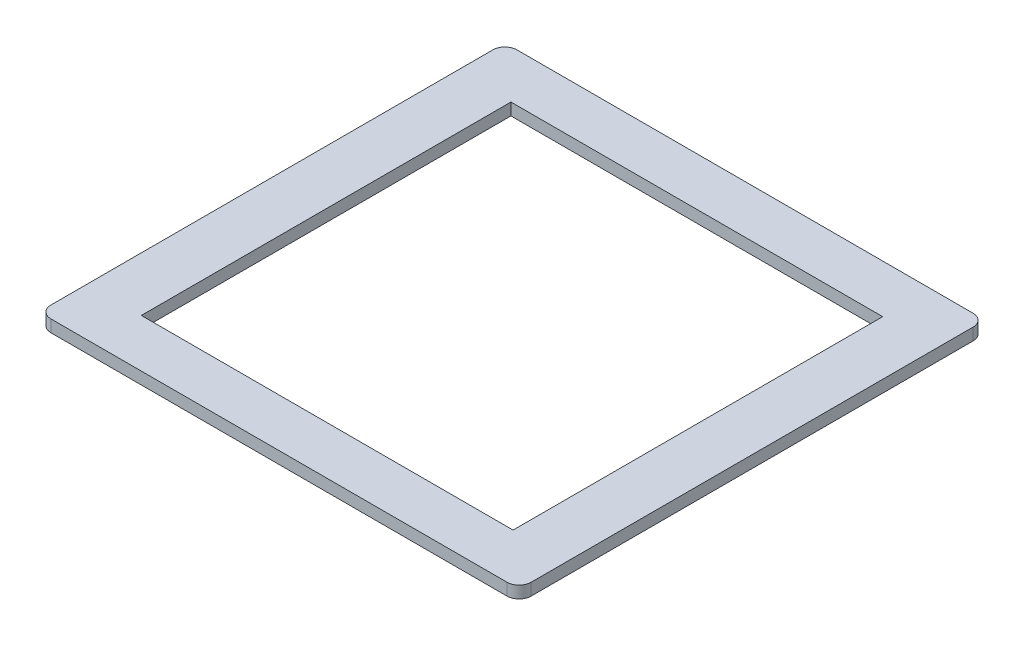
SolidWorks part; units mm, degrees
material "有机玻璃 (TM) GS 丙烯酸铸钣"
ref_plane "前视基准面" through (0, 0, 0) normal (0, 0, 1) x (1, 0, 0)
ref_plane "上视基准面" through (0, 0, 0) normal (0, 1, 0) x (1, 0, 0)
ref_plane "右视基准面" through (0, 0, 0) normal (1, 0, 0) x (0, 0, -1)
sketch "草图3" plane through (161.6806, -5752.5401, -301.1317) normal (0, 1, 0) x (1, 0, 0)
  line L0 (-111.2311, -179.1137) -> (-111.2311, -160.9249) construction
  line L1 (-111.2311, -160.9249) -> (-49.5289, -160.9249)
  line L2 (-111.2311, -160.9249) -> (-111.2311, -222.2721)
  line L3 (-111.2311, -222.2721) -> (-49.5289, -222.2721)
  line L4 (-49.5289, -160.9249) -> (-49.5289, -222.2721)
  line L5 (-49.5289, -179.1137) -> (-49.5289, -160.9249) construction
  line L6 (-112.2311, -222.2721) -> (-48.5289, -222.2721) construction
  line L7 (-111.2311, -160.9249) -> (-49.5289, -160.9249) construction
  line L8 (-120.2311, -154.9249) -> (-120.2311, -228.2721) construction
  line L9 (-118.2311, -152.9249) -> (-42.5289, -152.9249)
  line L10 (-120.2311, -154.9249) -> (-120.2311, -228.2721)
  line L11 (-118.2311, -230.2721) -> (-42.5289, -230.2721)
  line L12 (-40.5289, -154.9249) -> (-40.5289, -228.2721)
  line L13 (-40.5289, -154.9249) -> (-40.5289, -228.2721) construction
  line L14 (-118.2311, -152.9249) -> (-42.5289, -152.9249) construction
  line L15 (-118.2311, -230.2721) -> (-42.5289, -230.2721) construction
  arc A0 (-42.5289, -152.9249) -> (-40.5289, -154.9249) centre (-42.5289, -154.9249) cw
  arc A1 (-40.5289, -228.2721) -> (-42.5289, -230.2721) centre (-42.5289, -228.2721) cw
  arc A2 (-118.2311, -230.2721) -> (-120.2311, -228.2721) centre (-118.2311, -228.2721) cw
  arc A3 (-120.2311, -154.9249) -> (-118.2311, -152.9249) centre (-118.2311, -154.9249) cw
  dimension "D1" = 2
extrude "凸台-拉伸1" add sketch "草图3" along normal blind 2
